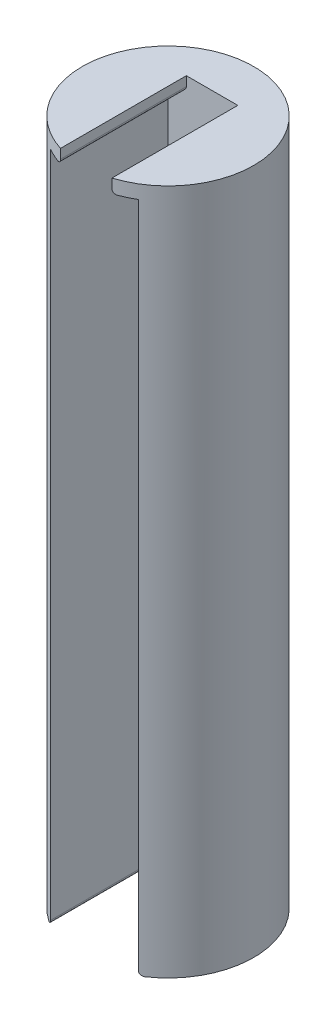
SolidWorks part; units mm, degrees
material "Alloy Steel"
ref_plane "Front Plane" through (0, 0, 0) normal (0, 0, 1) x (1, 0, 0)
ref_plane "Top Plane" through (0, 0, 0) normal (0, 1, 0) x (1, 0, 0)
ref_plane "Right Plane" through (0, 0, 0) normal (1, 0, 0) x (0, 0, -1)
sketch "cylinder_sketch" plane through (0, 0, 0) normal (0, 1, 0) x (1, 0, 0)
  circle A0 centre (0, 0) radius 6.35
  dimension "D1" = 12.7
extrude "cylinder" add sketch "cylinder_sketch" along normal blind 50.8
sketch "Sketch2" plane through (0, 0, 0) normal (0, 0, 1) x (1, 0, 0)
  line L0 (0, 0) -> (0, 50.8) construction
  line L1 (6.35, 50.8) -> (-6.35, 50.8) construction
  line L2 (-6.35, 0) -> (6.35, 0) construction
  line L3 (3.2639, 49.8) -> (-3.2639, 49.8)
  line L4 (3.2639, 49.8) -> (3.2639, 0)
  line L5 (3.2639, 0) -> (-3.2639, 0)
  line L6 (-3.2639, 49.8) -> (-3.2639, 0)
  line L7 (3.2639, 49.8) -> (-3.2639, 0) construction
  line L8 (3.2639, 0) -> (-3.2639, 49.8) construction
  line L10 (1.905, 50.8) -> (-1.905, 50.8)
  line L11 (1.905, 50.8) -> (1.905, 49.8)
  line L12 (1.905, 49.8) -> (-1.905, 49.8)
  line L13 (-1.905, 50.8) -> (-1.905, 49.8)
  line L14 (1.905, 50.8) -> (-1.905, 49.8) construction
  line L15 (1.905, 49.8) -> (-1.905, 50.8) construction
  point P5 (0, 24.9)
  point P12 (0, 50.3)
  point P17 (-1.7758, 50.8)
  point P18 (-3.2639, 47.8977)
  dimension "D1" = 6.5278
  dimension "D2" = 1
  dimension "D3" = 3.81
extrude "Cut-Extrude2" cut sketch "Sketch2" against normal blind 3.2639 and the other way up to next contours L3 L6 L5 L4 | L10 L13 L3 L11
fillet "Fillet1" radius 0.3 4 edges at (-3.2639, 0, 1.0915) (3.2639, 0, 1.0915) (1.905, 49.8, 1.3968) (-1.905, 49.8, 1.3968)
